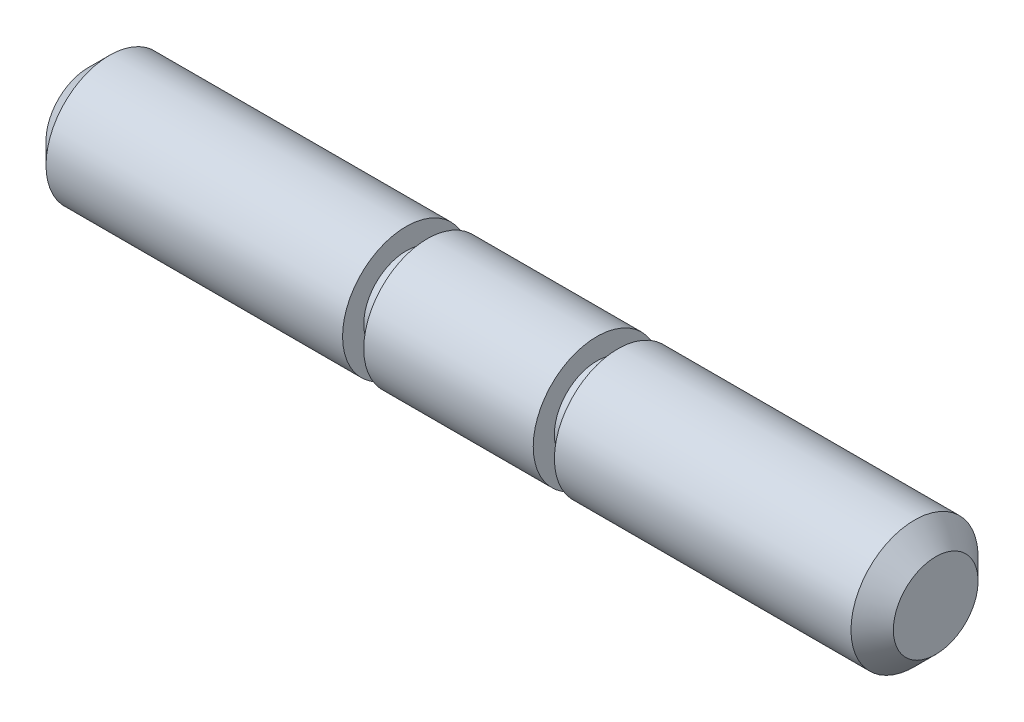
SolidWorks part; units mm, degrees
material "Plain Carbon Steel"
ref_plane "Front Plane" through (0, 0, 0) normal (0, 0, 1) x (1, 0, 0)
ref_plane "Top Plane" through (0, 0, 0) normal (0, 1, 0) x (1, 0, 0)
ref_plane "Right Plane" through (0, 0, 0) normal (1, 0, 0) x (0, 0, -1)
sketch "Sketch1" plane through (0, 0, 0) normal (0, 0, 1) x (1, 0, 0)
  line L0 (0, 0) -> (0, 10.4067) construction
  line L1 (-10, 1.5) -> (-2.5, 1.5)
  line L2 (-10, 1.5) -> (-10, 0)
  line L3 (-10, 0) -> (10, 0)
  line L4 (10, 1.5) -> (10, 0)
  line L5 (-2, 1.5) -> (2, 1.5)
  line L6 (2.5, 1.5) -> (10, 1.5)
  line L7 (-2.5, 1.5) -> (-2.5, 1)
  line L8 (-2.5, 1) -> (-2, 1)
  line L9 (-2, 1.5) -> (-2, 1)
  line L10 (0, 0) -> (43.9901, 0) construction
  line L11 (2, 1.5) -> (2, 1)
  line L12 (2, 1) -> (2.5, 1)
  line L13 (2.5, 1.5) -> (2.5, 1)
  dimension "D1" = 2
  dimension "D2" = 3
  dimension "D3" = 4
  dimension "D4" = 0.5
  dimension "D5" = 20
revolve "Revolve1" add sketch "Sketch1" angle 360 about L10
chamfer "Chamfer1" distance 0.5 angle 45 2 edges at (10, 0, 1.5) (-10, 0, 1.5)
